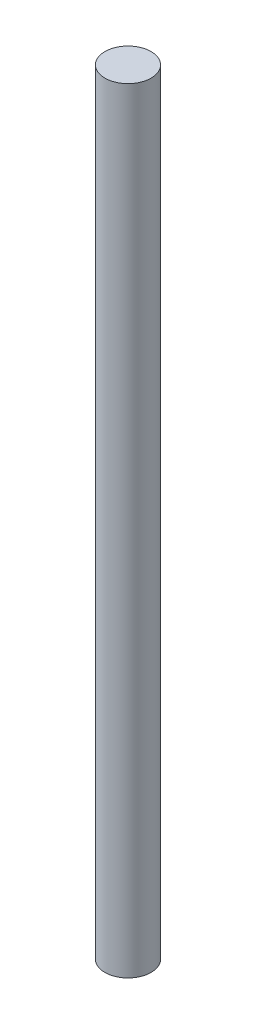
SolidWorks part; units mm, degrees
ref_plane "Front Plane" through (0, 0, 0) normal (0, 0, 1) x (1, 0, 0)
ref_plane "Top Plane" through (0, 0, 0) normal (0, 1, 0) x (1, 0, 0)
ref_plane "Right Plane" through (0, 0, 0) normal (1, 0, 0) x (0, 0, -1)
sketch "Sketch1" plane through (0, 0, 0) normal (0, 1, 0) x (1, 0, 0)
  circle A0 centre (0, 0) radius 4.7625
  dimension "D1" = 9.525
extrude "Boss-Extrude1" add sketch "Sketch1" along normal blind 160
